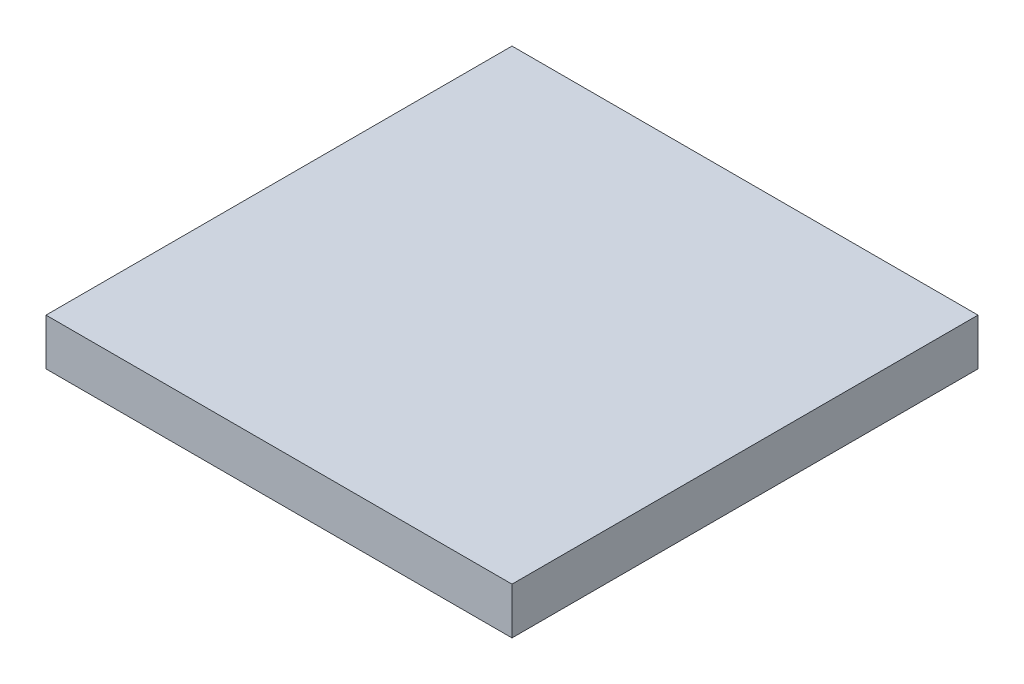
SolidWorks part; units mm, degrees
material "Pine"
ref_plane "Front Plane" through (0, 0, 0) normal (0, 0, 1) x (1, 0, 0)
ref_plane "Top Plane" through (0, 0, 0) normal (0, 1, 0) x (1, 0, 0)
ref_plane "Right Plane" through (0, 0, 0) normal (1, 0, 0) x (0, 0, -1)
sketch "Sketch1" plane through (0, 0, 0) normal (0, 1, 0) x (1, 0, 0)
  line L1 (127, -127) -> (-127, -127)
  line L2 (127, -127) -> (127, 127)
  line L3 (127, 127) -> (-127, 127)
  line L4 (-127, -127) -> (-127, 127)
  line L5 (127, -127) -> (-127, 127) construction
  line L6 (127, 127) -> (-127, -127) construction
  point P0 (0, 0)
  dimension "D1" = 254
extrude "Boss-Extrude2" add sketch "Sketch1" along normal blind 25.4
sketch "Sketch3" plane through (0, 0, 0) normal (0, 1, 0) x (1, 0, 0)
  line L0 (-127, 127) -> (-127, -127) construction
  line L1 (-114.3, 89.7128) -> (114.3, 89.7128)
  line L2 (-114.3, 89.7128) -> (-114.3, 88.9)
  line L3 (-114.3, 88.9) -> (114.3, 88.9)
  line L4 (114.3, 89.7128) -> (114.3, 88.9)
  line L5 (-114.3, 64.3128) -> (114.3, 64.3128)
  line L6 (-114.3, 64.3128) -> (-114.3, 63.5)
  line L7 (-114.3, 63.5) -> (114.3, 63.5)
  line L8 (114.3, 64.3128) -> (114.3, 63.5)
  line L9 (-114.3, 38.9128) -> (114.3, 38.9128)
  line L10 (-114.3, 38.9128) -> (-114.3, 38.1)
  line L11 (-114.3, 38.1) -> (114.3, 38.1)
  line L12 (114.3, 38.9128) -> (114.3, 38.1)
  line L13 (-114.3, 13.5128) -> (114.3, 13.5128)
  line L14 (-114.3, 13.5128) -> (-114.3, 12.7)
  line L15 (-114.3, 12.7) -> (114.3, 12.7)
  line L16 (114.3, 13.5128) -> (114.3, 12.7)
  line L17 (-181.9823, 0) -> (176.3676, 0) construction
  line L18 (114.3, -13.5128) -> (114.3, -12.7)
  line L19 (-114.3, -12.7) -> (114.3, -12.7)
  line L20 (-114.3, -13.5128) -> (-114.3, -12.7)
  line L21 (-114.3, -13.5128) -> (114.3, -13.5128)
  line L22 (114.3, -38.9128) -> (114.3, -38.1)
  line L23 (-114.3, -38.1) -> (114.3, -38.1)
  line L24 (-114.3, -38.9128) -> (-114.3, -38.1)
  line L25 (-114.3, -38.9128) -> (114.3, -38.9128)
  line L26 (114.3, -64.3128) -> (114.3, -63.5)
  line L27 (-114.3, -63.5) -> (114.3, -63.5)
  line L28 (-114.3, -64.3128) -> (-114.3, -63.5)
  line L29 (-114.3, -64.3128) -> (114.3, -64.3128)
  line L30 (114.3, -89.7128) -> (114.3, -88.9)
  line L31 (-114.3, -88.9) -> (114.3, -88.9)
  line L32 (-114.3, -89.7128) -> (-114.3, -88.9)
  line L33 (-114.3, -89.7128) -> (114.3, -89.7128)
  dimension "D1" = 12.7
  dimension "D2" = 25.4
  dimension "D3" = 25.4
  dimension "D4" = 25.4
  dimension "D5" = 228.6
  dimension "D6" = 12.7
  dimension "D7" = 0.8128
extrude "Cut-Extrude1" cut sketch "Sketch3" along normal blind 5.08
